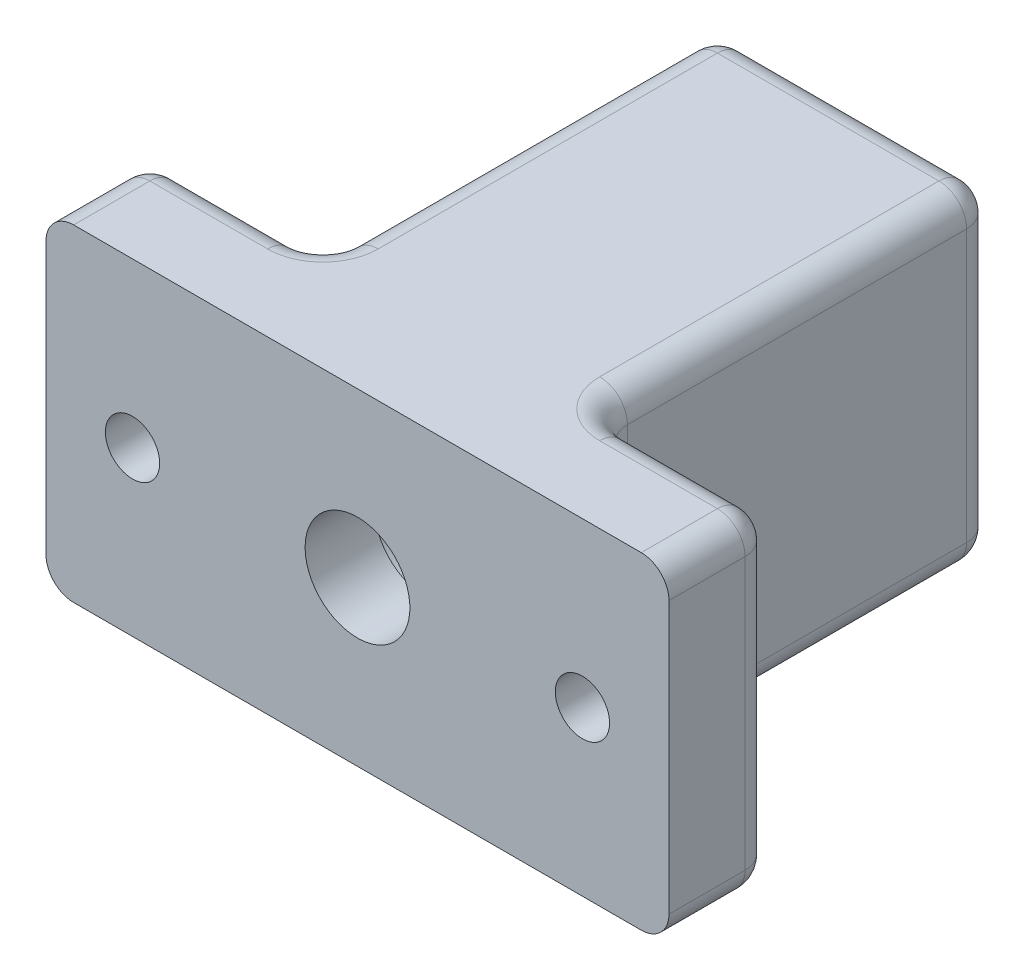
SolidWorks part; units mm, degrees
ref_plane "Front Plane" through (0, 0, 0) normal (0, 0, 1) x (1, 0, 0)
ref_plane "Top Plane" through (0, 0, 0) normal (0, 1, 0) x (1, 0, 0)
ref_plane "Right Plane" through (0, 0, 0) normal (1, 0, 0) x (0, 0, -1)
sketch "Sketch1" plane through (0, 0, 0) normal (0, 1, 0) x (1, 0, 0)
  line L0 (0, 0) -> (0, -35.0214) construction
  line L1 (4.8062, 6.35) -> (4.8062, 0)
  line L2 (4.8062, 0) -> (12.7, 0)
  line L3 (4.8062, 6.35) -> (6.7906, 6.35)
  line L4 (6.7906, 6.35) -> (6.7906, 41.91)
  line L5 (6.7906, 41.91) -> (4.7625, 41.91)
  line L6 (4.7625, 41.91) -> (4.7625, 45.72)
  line L7 (4.7625, 45.72) -> (12.7, 45.72)
  line L8 (12.7, 45.72) -> (12.7, 0)
  dimension "D1" = 9.6125
  dimension "D2" = 6.35
  dimension "D3" = 13.5812
  dimension "D4" = 41.91
  dimension "D5" = 3.81
  dimension "D6" = 9.525
  dimension "D7" = 25.4
revolve "Revolve1" add sketch "Sketch1" angle 360 about L0
sketch "Sketch3" plane through (0, 0, 0) normal (0, 0, -1) x (-1, 0, 0)
  line L1 (28.575, -15) -> (-28.575, -15)
  line L2 (28.575, -15) -> (28.575, 15)
  line L3 (28.575, 15) -> (-28.575, 15)
  line L4 (-28.575, -15) -> (-28.575, 15)
  line L5 (28.575, -15) -> (-28.575, 15) construction
  line L6 (28.575, 15) -> (-28.575, -15) construction
  circle A0 centre (0, 0) radius 12.7 construction
  circle A1 centre (0, 0) radius 12.7
  point P0 (0, 0)
  dimension "D1" = 57.15
  dimension "D2" = 30
extrude "Boss-Extrude1" add sketch "Sketch3" along normal blind 9.525
sketch "Sketch6" plane through (0, 0, -9.525) normal (0, 0, -1) x (-1, 0, 0)
  line L0 (-28.575, -15) -> (28.575, -15) construction
  line L1 (12.7, 15) -> (-12.7, 15)
  line L2 (12.7, 15) -> (12.7, -15)
  line L3 (12.7, -15) -> (-12.7, -15)
  line L4 (-12.7, 15) -> (-12.7, -15)
  line L5 (12.7, 15) -> (-12.7, -15) construction
  line L6 (12.7, -15) -> (-12.7, 15) construction
  circle A0 centre (0, 0) radius 12.7 construction
  circle A3 centre (0, 0) radius 11.684
  circle A4 centre (0, 0) radius 11.684
  point P0 (0, 0)
  dimension "D1" = 1.016
extrude "Boss-Extrude2" add sketch "Sketch6" along normal up to surface (36.195 mm away) up to face at (-4.7625, 0, -45.72)
hole_wizard "#10 Clearance Hole1" positions "Sketch5" profile "Sketch4" hole size "#10" standard "ANSI Inch" end condition through all
sketch "Sketch5" plane through (0, 0, -9.525) normal (0, 0, -1) x (-1, 0, 0)
  line L0 (0, 0) -> (-34.12, 0) construction
  line L1 (0, 0) -> (0, 36.1145) construction
  line L2 (28.575, -15) -> (28.575, 15) construction
  line L3 (12.7, -15) -> (12.7, 15) construction
  circle A0 centre (20.6375, 0) radius 7.9375 construction
  point P0 (20.6375, 0)
  point P16 (-20.6375, 0)
sketch "Sketch4" plane through (-20.6375, 0, -9.525) normal (1, 0, 0) x (0, 1, 0)
  line L0 (0, 0) -> (0, 9.525)
  line L1 (0, 9.525) -> (2.4892, 9.525)
  line L2 (2.4892, 9.525) -> (2.4892, 0)
  line L5 (2.4892, 0) -> (0, 0)
  line L11 (0, -6.35) -> (0, 107.95) construction
  dimension "Thru Hole Dia." = 4.9784
  dimension "Thru Hole Depth" = 9.525
fillet "Fillet2" radius 2.54 21 edges at (28.575, 15, -4.7625) (-28.575, 15, -4.7625) (-28.575, -15, -4.7625) (-20.6375, -15, -9.525) (20.6375, -15, -9.525) (-28.575, 0, -9.525) (28.575, 0, -9.525) (20.6375, 15, -9.525) (-20.6375, 15, -9.525) (28.575, -15, -4.7625) (-4.7625, 0, -45.72) (0, -15, -45.72) (12.7, 0, -9.525) (12.7, 0, -45.72) (0, 15, -45.72) (-12.7, 0, -9.525) (-12.7, 0, -45.72) (12.7, -15, -27.6225) (12.7, 15, -27.6225) (-12.7, 15, -27.6225) (-12.7, -15, -27.6225)
